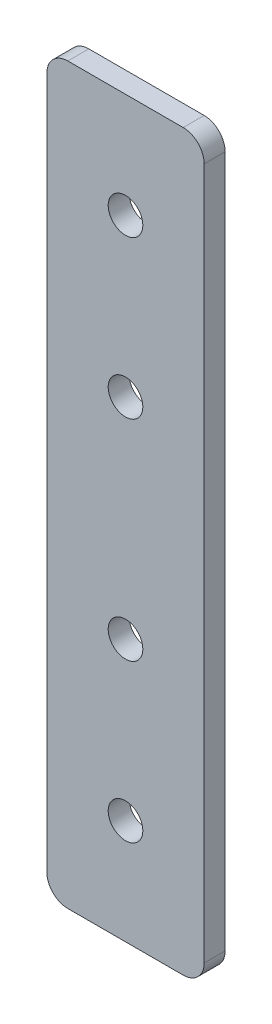
SolidWorks part; units mm, degrees
material "Простая углеродистая сталь"
ref_plane "Спереди" through (0, 0, 0) normal (0, 0, 1) x (1, 0, 0)
ref_plane "Сверху" through (0, 0, 0) normal (0, 1, 0) x (1, 0, 0)
ref_plane "Сбоку" through (0, 0, 0) normal (1, 0, 0) x (0, 0, -1)
sketch "Эскиз1" plane through (0, 0, 0) normal (0, 0, 1) x (1, 0, 0)
  line L1 (-7.5, -35) -> (7.5, -35)
  line L2 (-7.5, -35) -> (-7.5, 35)
  line L3 (-7.5, 35) -> (7.5, 35)
  line L4 (7.5, -35) -> (7.5, 35)
  line L5 (-7.5, -35) -> (7.5, 35) construction
  line L6 (-7.5, 35) -> (7.5, -35) construction
  point P0 (0, 0)
  dimension "D1" = 15
  dimension "D2" = 70
extrude "Бобышка-Вытянуть1" add sketch "Эскиз1" along normal blind 2
hole_wizard "Отверстие обработанное метчиком M41" positions "Эскиз2" profile "Эскиз3" tap size "M4" standard "DIN"
sketch "Эскиз2" plane through (0, 0, 2) normal (0, 0, 1) x (1, 0, 0)
  line L6 (0, 35) -> (0, -35) construction
  line L7 (7.5, 35) -> (-7.5, 35) construction
  line L8 (-7.5, -35) -> (7.5, -35) construction
  point P31 (0, -25)
  point P33 (0, -10)
  point P35 (0, 10)
  point P37 (0, 25)
  dimension "D1" = 10
  dimension "D2" = 10
  dimension "D3" = 15
  dimension "D4" = 15
sketch "Эскиз3" plane through (0, 25, 2) normal (1, 0, 0) x (0, -1, 0)
  line L0 (0, 0) -> (0, 12.4914)
  line L1 (0, 12.4914) -> (1.65, 11.5)
  line L2 (1.65, 11.5) -> (1.65, 0)
  line L5 (1.65, 0) -> (0, 0)
  line L10 (0, 12.4914) -> (-1.65, 11.5) construction
  line L11 (0, -6.35) -> (0, 107.95) construction
  dimension "Диаметр сверла" = 3.3
  dimension "Глубина сверла" = 11.5
  dimension "Угол заточки сверла" = 118
cosmetic thread "Отверстие резьбы2"
cosmetic thread "Отверстие резьбы3"
cosmetic thread "Отверстие резьбы4"
cosmetic thread "Отверстие резьбы5"
fillet "Скругление1" radius 2 4 edges at (-7.5, -35, 1) (7.5, -35, 1) (-7.5, 35, 1) (7.5, 35, 1)
